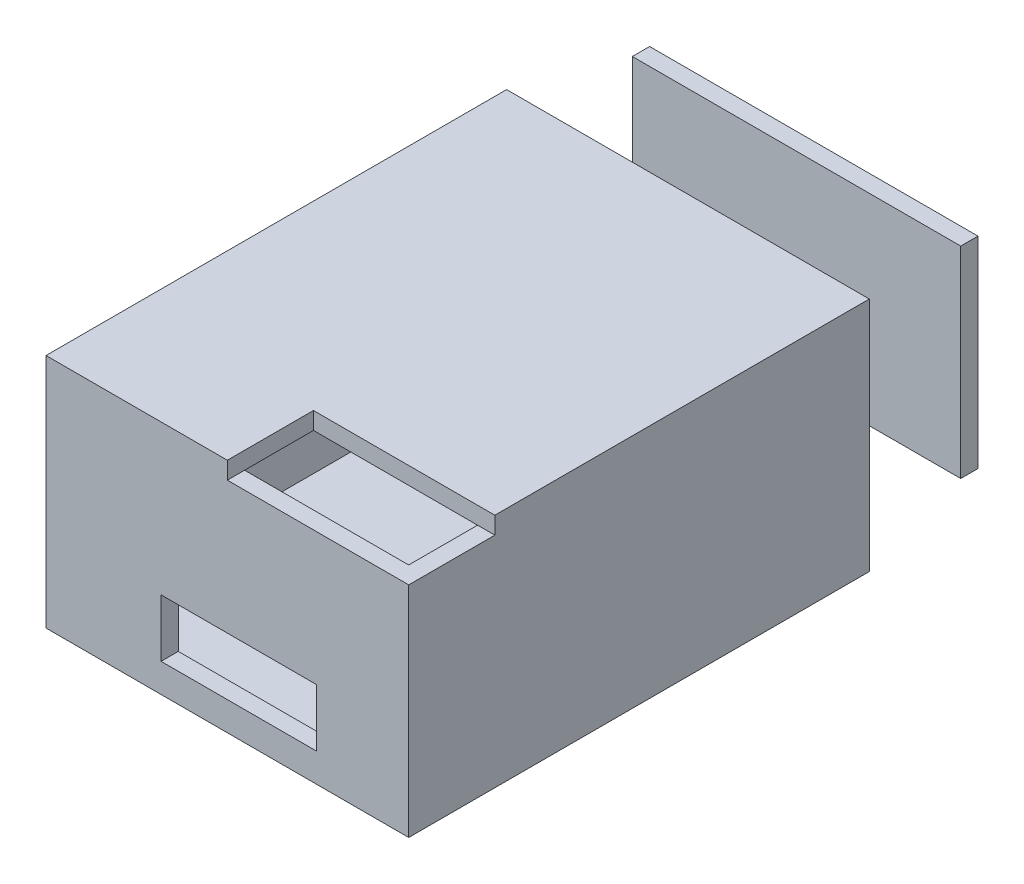
SolidWorks part; units mm, degrees
ref_plane "Plano frontal" through (0, 0, 0) normal (0, 0, 1) x (1, 0, 0)
ref_plane "Plano superior" through (0, 0, 0) normal (0, 1, 0) x (1, 0, 0)
ref_plane "Plano direito" through (0, 0, 0) normal (1, 0, 0) x (0, 0, -1)
sketch "Esboço2" plane through (0, 0, 0) normal (0, 1, 0) x (1, 0, 0)
  line L0 (0, 0) -> (63, 0)
  line L1 (63, 0) -> (63, -80)
  line L2 (63, -80) -> (0, -80)
  line L3 (0, -80) -> (0, 0)
  dimension "D1" = 63
  dimension "D2" = 80
extrude "Ressalto-extrusão1" add sketch "Esboço2" along normal blind 3
sketch "Esboço3" plane through (0, 3, 0) normal (0, 1, 0) x (1, 0, 0)
  line L0 (63, -80) -> (63, 0)
  line L1 (63, 0) -> (60.0017, 0)
  line L2 (63, 0) -> (0, 0) construction
  line L3 (60.0017, 0) -> (60.0017, -77.0106)
  line L4 (60.0017, -77.0106) -> (2.9904, -77.0106)
  line L5 (2.9904, -77.0106) -> (2.9904, 0)
  line L6 (2.9904, 0) -> (0, 0)
  line L7 (0, 0) -> (0, -80)
  line L8 (0, -80) -> (63, -80)
extrude "Ressalto-extrusão2" add sketch "Esboço3" along normal blind 35
sketch "Esboço4" plane through (0, 38, 0) normal (0, 1, 0) x (1, 0, 0)
  line L0 (63, 0) -> (63, -65.0418)
  line L1 (63, -80) -> (63, 0) construction
  line L2 (63, -65.0418) -> (0, -65.0418)
  line L3 (0, 0) -> (0, -80) construction
  line L4 (0, -65.0418) -> (0, 0)
  line L5 (0, 0) -> (63, 0)
extrude "Ressalto-extrusão3" add sketch "Esboço4" along normal blind 3
ref_plane "Plano4" through (0, 0, -20) normal (0, 0, -1) x (-1, 0, 0)
sketch "Esboço6" plane through (0, 0, -20) normal (0, 0, -1) x (-1, 0, 0)
  line L0 (-58.875, 36.8983) -> (-58.875, 1.9308)
  line L1 (-58.875, 1.9308) -> (-1.8364, 1.9308)
  line L2 (-1.8364, 1.9308) -> (-1.8364, 36.8983)
  line L3 (-1.8364, 36.8983) -> (-58.875, 36.8983)
extrude "Ressalto-extrusão4" add sketch "Esboço6" along normal blind 3 separate body
sketch "Esboço7" plane through (0, 38, 0) normal (0, 1, 0) x (1, 0, 0)
  line L0 (0, -65.0418) -> (0, -80)
  line L1 (0, -80) -> (31.5, -80)
  line L2 (0, -80) -> (63, -80) construction
  line L3 (31.5, -80) -> (31.496, -65.0418)
  line L4 (2.9904, -65.0418) -> (60.0017, -65.0418) construction
  line L5 (31.496, -65.0418) -> (0, -65.0418)
extrude "Ressalto-extrusão5" add sketch "Esboço7" along normal blind 3
sketch "Esboço8" plane through (0, 0, 80) normal (0, 0, 1) x (1, 0, 0)
  line L3 (19.9831, 4.9908) -> (46.9808, 4.9908)
  line L4 (46.9808, 4.9908) -> (46.9808, 14.9938)
  line L5 (46.9808, 14.9938) -> (19.9831, 14.9938)
  line L6 (19.9831, 14.9938) -> (19.9831, 4.9908)
extrude "Corte-extrusão1" cut sketch "Esboço8" against normal blind 3
